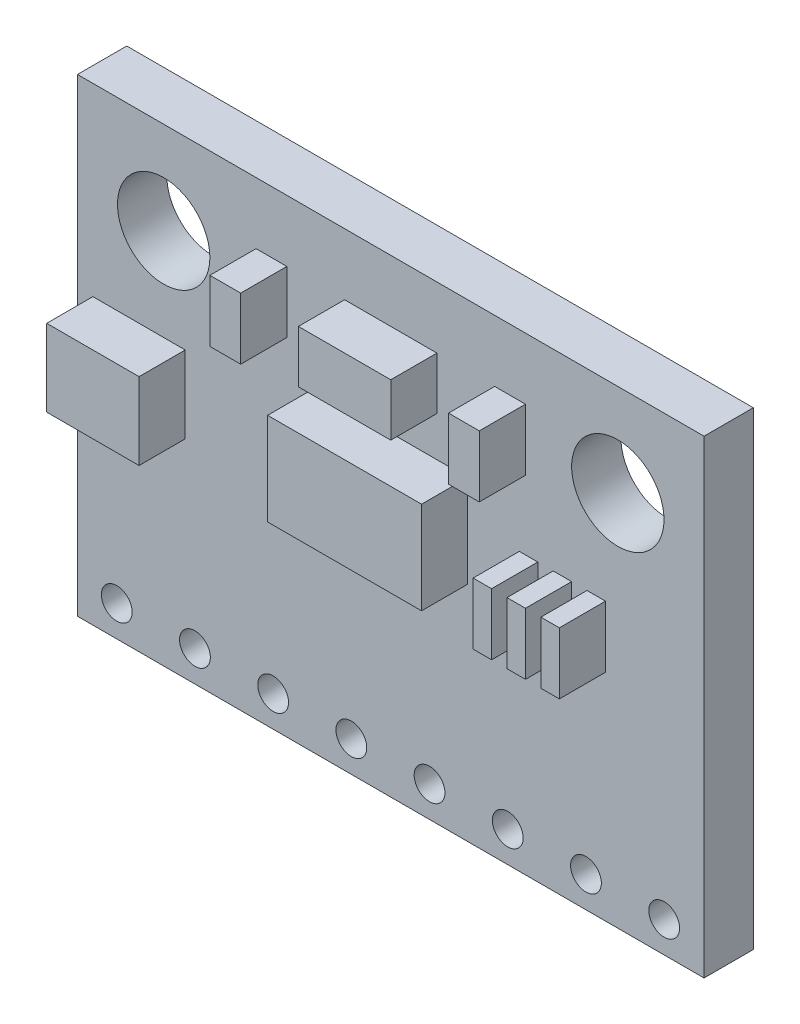
SolidWorks part; units mm, degrees
ref_plane "Front Plane" through (0, 0, 0) normal (0, 0, 1) x (1, 0, 0)
ref_plane "Top Plane" through (0, 0, 0) normal (0, 1, 0) x (1, 0, 0)
ref_plane "Right Plane" through (0, 0, 0) normal (1, 0, 0) x (0, 0, -1)
sketch "Sketch1" plane through (0, 0, 0) normal (0, 0, 1) x (1, 0, 0)
  line L0 (-7.375, 4.62) -> (7.375, 4.62) construction
  line L1 (-10.175, -7.62) -> (10.175, -7.62)
  line L2 (-10.175, -7.62) -> (-10.175, 7.62)
  line L3 (-10.175, 7.62) -> (10.175, 7.62)
  line L4 (10.175, -7.62) -> (10.175, 7.62)
  line L5 (-10.175, -7.62) -> (10.175, 7.62) construction
  line L6 (-10.175, 7.62) -> (10.175, -7.62) construction
  circle A0 centre (-7.375, 4.62) radius 1.5
  circle A1 centre (7.375, 4.62) radius 1.5
  point P0 (0, 0)
  point P10 (0, 4.62)
  point P11 (0, 0)
  point P12 (16.3082, 7.62)
  dimension "D2" = 3
  dimension "D3" = 3
  dimension "D1" = 15.24
  dimension "D4" = 3
  dimension "D5" = 14.75
  dimension "D6" = 20.35
  dimension "D7" = 2.8
extrude "Boss-Extrude1" add sketch "Sketch1" along normal blind 1.6
sketch "Sketch2" plane through (0, 0, 1.6) normal (0, 0, 1) x (1, 0, 0)
  line L0 (10.175, 7.62) -> (-10.175, 7.62) construction
  line L1 (-2.5, 2.62) -> (2.5, 2.62)
  line L2 (-2.5, 2.62) -> (-2.5, -0.38)
  line L3 (-2.5, -0.38) -> (2.5, -0.38)
  line L4 (2.5, 2.62) -> (2.5, -0.38)
  line L5 (-9.675, 1.62) -> (-6.675, 1.62)
  line L6 (-9.675, 1.62) -> (-9.675, -0.88)
  line L7 (-9.675, -0.88) -> (-6.675, -0.88)
  line L8 (-6.675, 1.62) -> (-6.675, -0.88)
  line L9 (-1.5, 5.62) -> (1.5, 5.62)
  line L10 (-1.5, 5.62) -> (-1.5, 3.92)
  line L11 (-1.5, 3.92) -> (1.5, 3.92)
  line L12 (1.5, 5.62) -> (1.5, 3.92)
  line L13 (3.375, 5.62) -> (4.375, 5.62)
  line L14 (3.375, 5.62) -> (3.375, 3.62)
  line L15 (3.375, 3.62) -> (4.375, 3.62)
  line L16 (4.375, 5.62) -> (4.375, 3.62)
  line L17 (-4.375, 5.62) -> (-3.375, 5.62)
  line L18 (-4.375, 5.62) -> (-4.375, 3.62)
  line L19 (-4.375, 3.62) -> (-3.375, 3.62)
  line L20 (-3.375, 5.62) -> (-3.375, 3.62)
  line L21 (4.175, 1.38) -> (4.775, 1.38)
  line L22 (4.175, 1.38) -> (4.175, -0.62)
  line L23 (4.175, -0.62) -> (4.775, -0.62)
  line L24 (4.775, 1.38) -> (4.775, -0.62)
  line L25 (5.275, 1.38) -> (5.875, 1.38)
  line L26 (5.275, 1.38) -> (5.275, -0.62)
  line L27 (5.275, -0.62) -> (5.875, -0.62)
  line L28 (5.875, 1.38) -> (5.875, -0.62)
  line L29 (6.375, 1.38) -> (6.975, 1.38)
  line L30 (6.375, 1.38) -> (6.375, -0.62)
  line L31 (6.375, -0.62) -> (6.975, -0.62)
  line L32 (6.975, 1.38) -> (6.975, -0.62)
  line L33 (-10.175, -7.62) -> (10.175, -7.62) construction
  line L34 (10.175, -7.62) -> (10.175, 7.62) construction
  line L35 (-10.175, 7.62) -> (-10.175, -7.62) construction
  point P32 (0, 5.62)
  point P33 (0, 0)
  point P35 (0, 2.62)
  point P42 (10.175, 0)
  point P43 (7.5096, -0.62)
  point P44 (6.0852, -0.62)
  dimension "D1" = 3
  dimension "D2" = 5
  dimension "D3" = 5
  dimension "D4" = 3
  dimension "D5" = 0.6
  dimension "D6" = 7
  dimension "D7" = 2
  dimension "D8" = 6
  dimension "D9" = 0.5
  dimension "D10" = 0.5
  dimension "D11" = 2.5
  dimension "D12" = 3
  dimension "D13" = 6
  dimension "D14" = 0.5
  dimension "D15" = 2
  dimension "D16" = 1.7
  dimension "D17" = 2
  dimension "D18" = 5.8
  dimension "D19" = 5.8
  dimension "D20" = 1
extrude "Boss-Extrude2" add sketch "Sketch2" along normal blind 1.5
sketch "Sketch3" plane through (0, 0, 1.6) normal (0, 0, 1) x (1, 0, 0)
  line L0 (-10.175, -7.62) -> (10.175, -7.62) construction
  circle A0 centre (-1.28, -6.62) radius 0.5
  point P6 (0, 0)
  dimension "D1" = 1
  dimension "D2" = 7.62
  dimension "D3" = 1.28
  dimension "D4" = 1
extrude "Cut-Extrude1" cut sketch "Sketch3" against normal through all
pattern_linear "LPattern1" count 5 spacing 2.54 along (1, 0, 0) count 4 spacing 2.54 along (-1, 0, 0) of "Cut-Extrude1"
